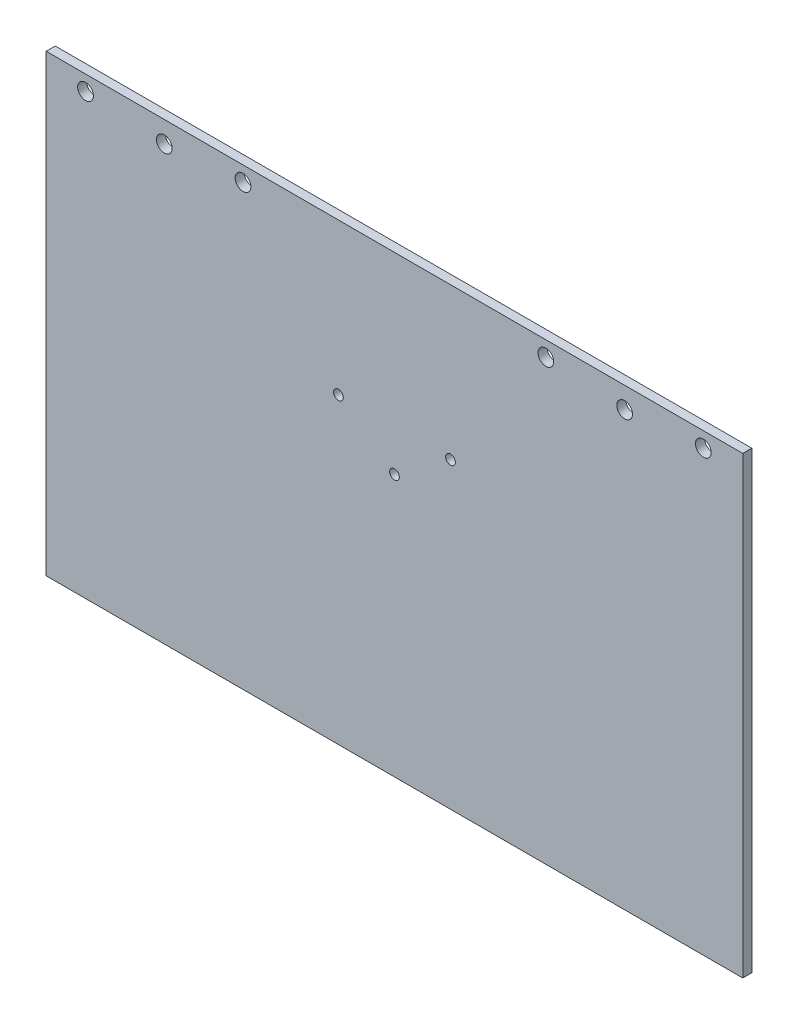
SolidWorks part; units mm, degrees
material "Acrylic (Medium-high impact)"
ref_plane "前视基准面" through (0, 0, 0) normal (0, 0, 1) x (1, 0, 0)
ref_plane "上视基准面" through (0, 0, 0) normal (0, 1, 0) x (1, 0, 0)
ref_plane "右视基准面" through (0, 0, 0) normal (1, 0, 0) x (0, 0, -1)
sketch "草图1" plane through (0, 0, 0) normal (0, 0, 1) x (1, 0, 0)
  line L0 (85, -50) -> (-145, -50)
  line L1 (-145, 100) -> (85, 100)
  line L2 (-145, 100) -> (-145, -50)
  line L4 (85, 100) -> (85, -50)
  line L5 (-145, 100) -> (71.0836, -49.0231) construction
  line L6 (-73.8926, -86.9324) -> (85, 100) construction
  point P0 (0, 0)
  dimension "D1" = 230
  dimension "D2" = 200
  dimension "D3" = 150
extrude "凸台-拉伸1" add sketch "草图1" along normal blind 3
sketch "草图7" plane through (0, 0, 0) normal (0, 0, -1) x (-1, 0, 0)
  line L0 (30, 16.3525) -> (30, 100) construction
  line L1 (-85, 100) -> (145, 100) construction
  line L2 (-20, 95) -> (-72, 95) construction
  line L3 (-85, 100) -> (145, 100) construction
  line L4 (-46, 93) -> (-46, 95) construction
  circle A0 centre (-20, 95) radius 2.6
  circle A1 centre (-72, 95) radius 2.6
  circle A2 centre (-46, 93) radius 2.6
  circle A3 centre (132, 95) radius 2.6
  circle A4 centre (106, 93) radius 2.6
  circle A5 centre (80, 95) radius 2.6
  dimension "D1" = 5
  dimension "D2" = 50
  dimension "D3" = 52
  dimension "D4" = 7
  dimension "D5" = 5.2
extrude "切除-拉伸4" cut sketch "草图7" against normal blind 10
sketch "Sketch1" plane through (0, 0, 3) normal (0, 0, 1) x (1, 0, 0)
  circle A3 centre (-30, 36.5) radius 1.6
  circle A4 centre (-11.5, 50) radius 1.6
  circle A5 centre (-48.5, 50) radius 1.6
extrude "Cut-Extrude1" cut sketch "Sketch1" against normal blind 10
